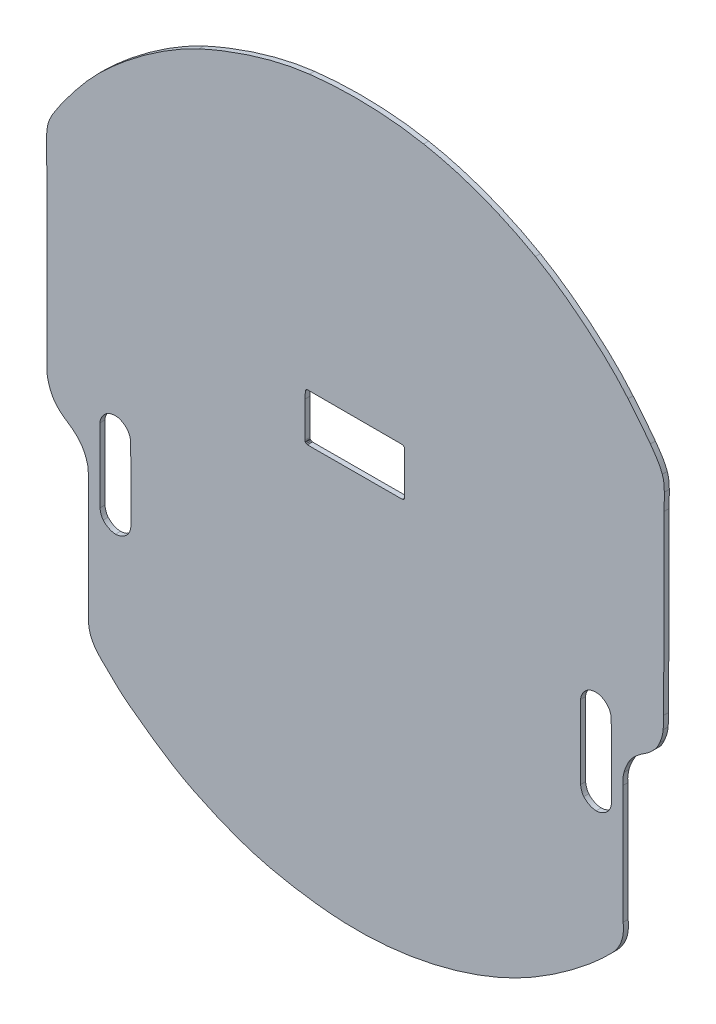
SolidWorks part; units mm, degrees
ref_plane "Front Plane" through (0, 0, 0) normal (0, 0, 1) x (1, 0, 0)
ref_plane "Top Plane" through (0, 0, 0) normal (0, 1, 0) x (1, 0, 0)
ref_plane "Right Plane" through (0, 0, 0) normal (1, 0, 0) x (0, 0, -1)
sketch "Model" plane through (0, 0, 0) normal (0, 0, 1) x (1, 0, 0)
  line L0 (193.4277, 350.0683) -> (193.3569, 345.5348)
  line L1 (193.3569, 345.5348) -> (193.3333, 323.3869)
  line L2 (193.3333, 323.3869) -> (193.3805, 322.5842)
  line L3 (193.3805, 322.5842) -> (193.5458, 322.2536)
  line L4 (193.5458, 322.2536) -> (193.9944, 321.923)
  line L5 (193.9944, 321.923) -> (194.4194, 321.7577)
  line L6 (194.4194, 321.7577) -> (194.7736, 321.5925)
  line L7 (194.7736, 321.5925) -> (253.4127, 321.7663)
  line L8 (253.4127, 321.7663) -> (253.8301, 321.783)
  line L9 (253.8301, 321.783) -> (254.3643, 321.9833)
  line L10 (254.3643, 321.9833) -> (254.6983, 322.3173)
  line L11 (254.6983, 322.3173) -> (254.9821, 322.7681)
  line L12 (254.9821, 322.7681) -> (255.0489, 323.4526)
  line L13 (255.0489, 323.4526) -> (255.1324, 349.632)
  line L14 (255.1324, 349.632) -> (254.9654, 350.1997)
  line L15 (254.9654, 350.1997) -> (254.5814, 350.6505)
  line L16 (254.5814, 350.6505) -> (254.0805, 351.0011)
  line L17 (254.0805, 351.0011) -> (253.4294, 351.118)
  line L18 (253.4294, 351.118) -> (252.3608, 351.168)
  line L19 (252.3608, 351.168) -> (195.4857, 351.1931)
  line L20 (195.4857, 351.1931) -> (194.9431, 351.2015)
  line L21 (194.9431, 351.2015) -> (194.5674, 351.1264)
  line L22 (194.5674, 351.1264) -> (194.3087, 351.0429)
  line L23 (194.3087, 351.0429) -> (194.0081, 350.8342)
  line L24 (194.0081, 350.8342) -> (193.7243, 350.5754)
  line L25 (193.7243, 350.5754) -> (193.4989, 350.2415)
  line L26 (193.4989, 350.2415) -> (193.4277, 350.0683)
  line L27 (32.9914, 407.584) -> (33.2275, 281.5818)
  line L28 (58.8288, 236.7304) -> (58.8841, 161.5166)
  line L29 (390.6333, 163.0157) -> (390.4204, 236.3493)
  line L30 (415.7562, 286.7415) -> (416.0916, 396.4891)
  line L31 (416.0916, 396.4891) -> (416.1812, 406.8546)
  spline S0 degree 2 poles (33.2275, 281.5818) (32.8687, 277.5273) (35.3067, 271.3323) knots 0 0 0 1 1 1
  spline S1 degree 3 poles (35.3067, 271.3323) (37.0279, 266.9586) (39.985, 263.1655) (46.2198, 259.1695) knots 0 0 0 0 1 1 1 1
  spline S2 degree 3 poles (46.2198, 259.1695) (49.1671, 257.2805) (52.0048, 254.8779) (54.0617, 252.1776) knots 0 0 0 0 1 1 1 1
  spline S3 degree 3 poles (54.0617, 252.1776) (55.1788, 250.7113) (55.744, 249.6363) (56.7108, 247.5178) knots 0 0 0 0 1 1 1 1
  spline S4 degree 3 poles (56.7108, 247.5178) (57.3417, 246.1353) (57.2607, 246.5336) (58.1751, 243.4731) knots 0 0 0 0 1 1 1 1
  spline S5 degree 3 poles (58.1751, 243.4731) (58.2459, 243.2361) (58.4753, 242.6438) (58.5875, 241.7568) knots 0 0 0 0 1 1 1 1
  spline S6 degree 3 poles (58.5875, 241.7568) (58.7521, 240.4554) (58.799, 238.5773) (58.8288, 236.7304) knots 0 0 0 0 1 1 1 1
  spline S7 degree 2 poles (58.8841, 161.5166) (58.8962, 157.5577) (59.1611, 156.0327) knots 0 0 0 1 1 1
  spline S8 degree 3 poles (59.1611, 156.0327) (59.4774, 154.2116) (60.0691, 152.0834) (60.9646, 150.242) knots 0 0 0 0 1 1 1 1
  spline S9 degree 3 poles (60.9646, 150.242) (63.1316, 145.7857) (65.6778, 143.3623) (69.3115, 139.9673) knots 0 0 0 0 1 1 1 1
  spline S10 degree 3 poles (69.3115, 139.9673) (74.1488, 135.4478) (78.0804, 130.9727) (83.7061, 126.8128) knots 0 0 0 0 1 1 1 1
  spline S11 degree 3 poles (83.7061, 126.8128) (93.9425, 119.2435) (108.2101, 108.3491) (124.3289, 100.4) knots 0 0 0 0 1 1 1 1
  spline S12 degree 3 poles (124.3289, 100.4) (138.7706, 93.278) (154.5069, 86.7846) (171.3343, 82.8182) knots 0 0 0 0 1 1 1 1
  spline S13 degree 3 poles (171.3343, 82.8182) (184.8448, 79.6337) (201.8573, 77.0413) (218.054, 76.3693) knots 0 0 0 0 1 1 1 1
  spline S14 degree 3 poles (218.054, 76.3693) (258.6842, 74.6835) (301.6467, 86.3362) (334.3725, 105.3519) knots 0 0 0 0 1 1 1 1
  spline S15 degree 3 poles (334.3725, 105.3519) (355.2249, 117.4684) (373.1835, 132.1556) (383.8462, 143.2214) knots 0 0 0 0 1 1 1 1
  spline S16 degree 2 poles (383.8462, 143.2214) (392.0354, 151.7203) (390.6333, 163.0157) knots 0 0 0 1 1 1
  spline S17 degree 2 poles (390.4204, 236.3493) (390.1865, 239.7832) (391.1556, 243.8529) knots 0 0 0 1 1 1
  spline S18 degree 3 poles (391.1556, 243.8529) (391.6877, 246.0877) (392.8393, 248.3977) (393.9918, 250.7086) knots 0 0 0 0 1 1 1 1
  spline S19 degree 3 poles (393.9918, 250.7086) (395.0881, 252.9065) (396.8135, 254.747) (398.5748, 256.3644) knots 0 0 0 0 1 1 1 1
  spline S20 degree 3 poles (398.5748, 256.3644) (400.0304, 257.701) (402.857, 259.7107) (404.8339, 260.9326) knots 0 0 0 0 1 1 1 1
  spline S21 degree 3 poles (404.8339, 260.9326) (407.1927, 262.3904) (408.0811, 263.5239) (408.8701, 264.3312) knots 0 0 0 0 1 1 1 1
  spline S22 degree 3 poles (408.8701, 264.3312) (410.1589, 265.6498) (410.7265, 266.1186) (411.0479, 266.597) knots 0 0 0 0 1 1 1 1
  spline S23 degree 3 poles (411.0479, 266.597) (412.0597, 268.103) (412.8978, 269.9373) (413.2493, 270.6969) knots 0 0 0 0 1 1 1 1
  spline S24 degree 3 poles (413.2493, 270.6969) (414.8582, 274.1735) (415.3366, 277.2723) (415.4783, 278.8454) knots 0 0 0 0 1 1 1 1
  spline S25 degree 2 poles (415.4783, 278.8454) (415.8324, 282.7755) (415.7562, 286.7415) knots 0 0 0 1 1 1
  spline S26 degree 3 poles (416.1812, 406.8546) (416.0803, 410.496) (416.0171, 412.6671) (414.9215, 415.8559) knots 0 0 0 0 1 1 1 1
  spline S27 degree 3 poles (414.9215, 415.8559) (413.3364, 420.4689) (410.4032, 424.4081) (407.5434, 428.4813) knots 0 0 0 0 1 1 1 1
  spline S28 degree 3 poles (407.5434, 428.4813) (403.4267, 434.3447) (398.5356, 439.8985) (393.6824, 445.8614) knots 0 0 0 0 1 1 1 1
  spline S29 degree 3 poles (393.6824, 445.8614) (380.5915, 461.9456) (356.4697, 481.8483) (336.2094, 493.505) knots 0 0 0 0 1 1 1 1
  spline S30 degree 3 poles (336.2094, 493.505) (315.9107, 505.1836) (292.3581, 514.5083) (266.8631, 519.3007) knots 0 0 0 0 1 1 1 1
  spline S31 degree 3 poles (266.8631, 519.3007) (243.9805, 523.6021) (219.4292, 524.1357) (195.9988, 521.3978) knots 0 0 0 0 1 1 1 1
  spline S32 degree 3 poles (195.9988, 521.3978) (175.1134, 518.9573) (150.6178, 511.4253) (127.3611, 500.6494) knots 0 0 0 0 1 1 1 1
  spline S33 degree 3 poles (127.3611, 500.6494) (111.7831, 493.4315) (87.5848, 478.3471) (65.3415, 456.4975) knots 0 0 0 0 1 1 1 1
  spline S34 degree 3 poles (65.3415, 456.4975) (57.573, 448.8665) (50.0169, 439.3323) (43.091, 429.8542) knots 0 0 0 0 1 1 1 1
  spline S35 degree 3 poles (43.091, 429.8542) (42.1147, 428.5182) (41.2599, 427.1152) (40.2916, 425.7608) knots 0 0 0 0 1 1 1 1
  spline S36 degree 3 poles (40.2916, 425.7608) (38.9969, 423.95) (37.7463, 422.0619) (36.7104, 420.2205) knots 0 0 0 0 1 1 1 1
  spline S37 degree 3 poles (36.7104, 420.2205) (35.9932, 418.9458) (36.4441, 419.9034) (34.7192, 416.2779) knots 0 0 0 0 1 1 1 1
  spline S38 degree 3 poles (34.7192, 416.2779) (34.6161, 416.0611) (33.8972, 414.1564) (33.6359, 412.8967) knots 0 0 0 0 1 1 1 1
  spline S39 degree 3 poles (33.6359, 412.8967) (33.2827, 411.1937) (33.0216, 409.9358) (32.9914, 407.584) knots 0 0 0 0 1 1 1 1
  spline S40 degree 3 poles (225.4634, 213.9098) (225.4634, 210.8541) (223.073, 208.3466) (220.0552, 208.2368) knots 0 0 0 0 1 1 1 1
  spline S41 degree 3 poles (220.0552, 208.2368) (217.0373, 208.127) (214.4751, 210.4543) (214.2582, 213.5021) knots 0 0 0 0 1 1 1 1
  spline S42 degree 3 poles (214.2582, 213.5021) (214.0413, 216.5499) (216.2476, 219.2246) (219.2499, 219.5534) knots 0 0 0 0 1 1 1 1
  spline S43 degree 3 poles (219.2499, 219.5534) (222.2521, 219.8823) (224.9729, 217.7473) (225.4056, 214.7231) knots 0 0 0 0 1 1 1 1
  spline S44 degree 3 poles (75.4632, 277.6273) (68.8885, 277.7346) (66.0375, 271.6517) (66.0185, 269.0326) knots 0 0 0 0 1 1 1 1
  spline S45 degree 3 poles (66.0185, 269.0326) (65.908, 253.8113) (66.1616, 238.5889) (66.0657, 223.3674) knots 0 0 0 0 1 1 1 1
  spline S46 degree 3 poles (66.0657, 223.3674) (66.0602, 222.4789) (66.7066, 219.302) (68.0019, 217.8423) knots 0 0 0 0 1 1 1 1
  spline S47 degree 3 poles (68.0019, 217.8423) (69.899, 215.7045) (72.8414, 214.0991) (75.6993, 214.0644) knots 0 0 0 0 1 1 1 1
  spline S48 degree 3 poles (75.6993, 214.0644) (78.3685, 214.032) (81.1719, 215.446) (82.9718, 217.4173) knots 0 0 0 0 1 1 1 1
  spline S49 degree 3 poles (82.9718, 217.4173) (84.5261, 219.1196) (85.2355, 221.6278) (85.2857, 223.9341) knots 0 0 0 0 1 1 1 1
  spline S50 degree 3 poles (85.2857, 223.9341) (85.6107, 238.8535) (85.0621, 267.249) (85.0024, 268.7021) knots 0 0 0 0 1 1 1 1
  spline S51 degree 3 poles (85.0024, 268.7021) (84.9426, 270.1552) (84.4495, 271.7371) (83.6329, 272.9994) knots 0 0 0 0 1 1 1 1
  spline S52 degree 3 poles (83.6329, 272.9994) (82.6339, 274.5437) (81.259, 275.8275) (79.5245, 276.6828) knots 0 0 0 0 1 1 1 1
  spline S53 degree 3 poles (79.5245, 276.6828) (77.6037, 277.63) (76.8529, 277.6047) (75.4632, 277.6273) knots 0 0 0 0 1 1 1 1
  spline S54 degree 3 poles (373.662, 278.0991) (367.0872, 278.2064) (364.2363, 272.1235) (364.2173, 269.5044) knots 0 0 0 0 1 1 1 1
  spline S55 degree 3 poles (364.2173, 269.5044) (364.1068, 254.2831) (364.3603, 239.0607) (364.2645, 223.8393) knots 0 0 0 0 1 1 1 1
  spline S56 degree 3 poles (364.2645, 223.8393) (364.2589, 222.9507) (364.9053, 219.7738) (366.2006, 218.3141) knots 0 0 0 0 1 1 1 1
  spline S57 degree 3 poles (366.2006, 218.3141) (368.0977, 216.1763) (371.0401, 214.5709) (373.8981, 214.5362) knots 0 0 0 0 1 1 1 1
  spline S58 degree 3 poles (373.8981, 214.5362) (376.5672, 214.5038) (379.3706, 215.9178) (381.1705, 217.8891) knots 0 0 0 0 1 1 1 1
  spline S59 degree 3 poles (381.1705, 217.8891) (382.7248, 219.5914) (383.4342, 222.0996) (383.4844, 224.4059) knots 0 0 0 0 1 1 1 1
  spline S60 degree 3 poles (383.4844, 224.4059) (383.8094, 239.3253) (383.2609, 267.7208) (383.2011, 269.1739) knots 0 0 0 0 1 1 1 1
  spline S61 degree 3 poles (383.2011, 269.1739) (383.1414, 270.627) (382.6482, 272.2089) (381.8316, 273.4712) knots 0 0 0 0 1 1 1 1
  spline S62 degree 3 poles (381.8316, 273.4712) (380.8326, 275.0155) (379.4577, 276.2993) (377.7232, 277.1546) knots 0 0 0 0 1 1 1 1
  spline S63 degree 3 poles (377.7232, 277.1546) (375.8024, 278.1019) (375.0516, 278.0765) (373.662, 278.0991) knots 0 0 0 0 1 1 1 1
extrude "Boss-Extrude1" add sketch "Model" along normal blind 3.09
